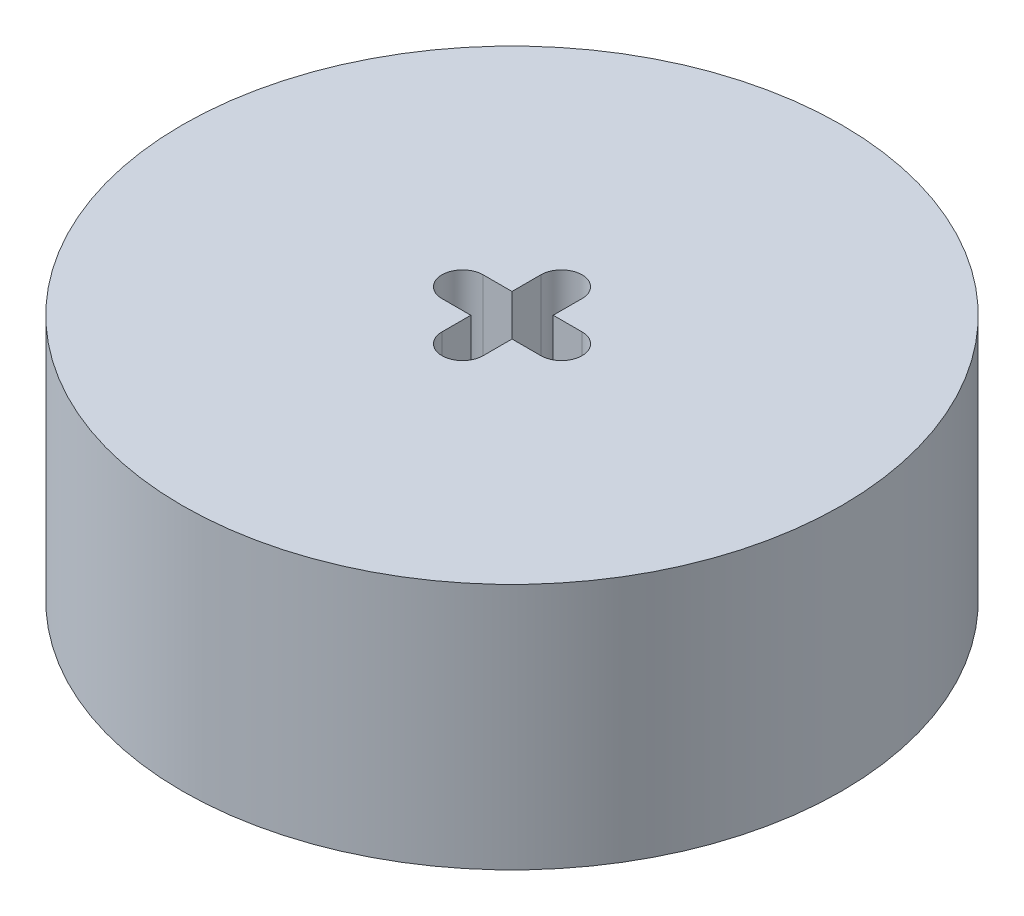
SolidWorks part; units mm, degrees
ref_plane "Front Plane" through (0, 0, 0) normal (0, 0, 1) x (1, 0, 0)
ref_plane "Top Plane" through (0, 0, 0) normal (0, 1, 0) x (1, 0, 0)
ref_plane "Right Plane" through (0, 0, 0) normal (1, 0, 0) x (0, 0, -1)
sketch "Sketch1" plane through (0, 0, 0) normal (0, 1, 0) x (1, 0, 0)
  circle A0 centre (0, 0) radius 50.8
  circle A1 centre (0, 0) radius 3.175
  dimension "D1" = 6.35
  dimension "D2" = 101.6
extrude "Boss-Extrude1" add sketch "Sketch1" along normal blind 38.1
sketch "Sketch2" plane through (0, 38.1, 0) normal (0, 1, 0) x (1, 0, 0)
  line L0 (0, 3.174) -> (0, 3.176) construction
  line L1 (-3.175, 3.174) -> (-3.175, 7.62)
  line L4 (3.175, 3.176) -> (7.621, 3.176)
  line L7 (3.177, -3.174) -> (3.177, -7.62)
  line L10 (-3.173, -3.176) -> (-7.619, -3.176)
  line L11 (0.001, 3.174) -> (0, 3.174)
  line L12 (-3.173, -3.176) -> (-3.173, -7.62)
  line L13 (3.177, -3.174) -> (7.621, -3.174)
  line L14 (3.175, 3.176) -> (3.175, 7.62)
  line L15 (-3.175, 3.174) -> (-7.619, 3.174)
  arc A1 (3.175, 7.62) -> (-3.175, 7.62) centre (0, 7.62) ccw
  arc A3 (0.001, 3.176) -> (0, 3.176) centre (0.001, 0.001) ccw
  arc A4 (7.621, -3.174) -> (7.621, 3.176) centre (7.621, 0.001) ccw
  arc A6 (-3.173, -7.62) -> (3.177, -7.62) centre (0.002, -7.62) ccw
  arc A8 (-7.619, 3.174) -> (-7.619, -3.176) centre (-7.619, -0.001) ccw
  point P2 (0, 3.81)
  circle M7 centre (0, 0) radius 3.175
extrude "Cut-Extrude1" cut sketch "Sketch2" against normal through all contours L15 A8 L10 M7 | L14 A1 L1 M7 | L13 A4 L4 M7 | L12 A6 L7 M7
